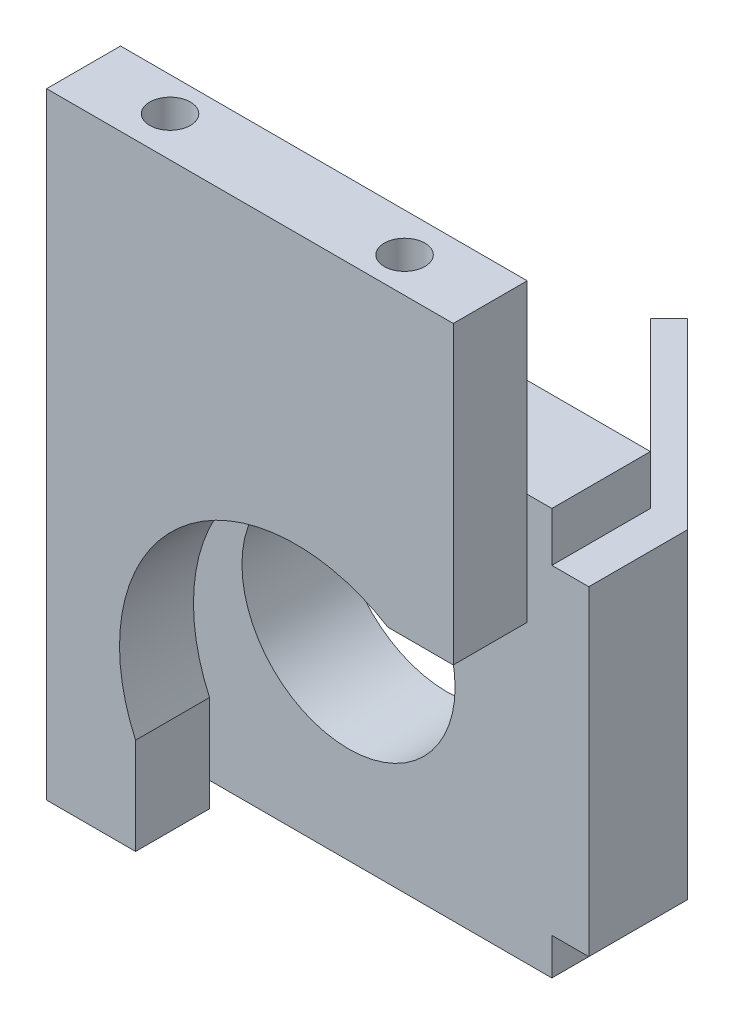
SolidWorks part; units mm, degrees
ref_plane "Front Plane" through (0, 0, 0) normal (0, 0, 1) x (1, 0, 0)
ref_plane "Top Plane" through (0, 0, 0) normal (0, 1, 0) x (1, 0, 0)
ref_plane "Right Plane" through (0, 0, 0) normal (1, 0, 0) x (0, 0, -1)
sketch "Sketch2" plane through (0, 0, 0) normal (0, 0, 1) x (1, 0, 0)
  line L1 (0, 0) -> (33, 0)
  line L2 (0, 0) -> (0, 33)
  line L3 (0, 33) -> (33, 33)
  line L4 (33, 0) -> (33, 33)
  circle A0 centre (16.5, 16.5) radius 8.65
  point P8 (16.5, 0)
  point P10 (0, 16.5)
  dimension "D3" = 17.3
  dimension "D1" = 33
  dimension "D2" = 33
extrude "Boss-Extrude1" add sketch "Sketch2" along normal blind 8
sketch "Sketch3" plane through (33, 0, 0) normal (1, 0, 0) x (0, 0, -1)
  line L0 (-8, 0) -> (-8, 33) construction
  line L1 (-8, 3) -> (0, 3)
  line L2 (-8, 3) -> (-8, 29)
  line L3 (-8, 29) -> (0, 29)
  line L4 (0, 3) -> (0, 29)
  line L5 (0, 0) -> (0, 33) construction
  line L6 (-8, 0) -> (0, 0) construction
  dimension "D1" = 26
  dimension "D2" = 3
extrude "Boss-Extrude2" add sketch "Sketch3" along normal blind 3
ref_plane "Plane1" through (16.5, 0, -16.5) normal (0.7071, 0, -0.7071) x (0, 1, 0)
sketch "Sketch4" plane through (16.5, 0, -16.5) normal (0.7071, 0, -0.7071) x (0, 1, 0)
  line L1 (3, 25.4558) -> (29, 25.4558)
  line L2 (3, 25.4558) -> (3, 4.4558)
  line L3 (3, 4.4558) -> (29, 4.4558)
  line L4 (29, 25.4558) -> (29, 4.4558)
  circle A0 centre (16, 14.9558) radius 8.1
  dimension "D3" = 16.2
  dimension "D1" = 21
  dimension "D2" = 26
  dimension "D4" = 10.5
  dimension "D5" = 13
extrude "Boss-Extrude3" add sketch "Sketch4" along normal blind 2.12
sketch "Sketch5" plane through (0, 0, 8) normal (0, 0, 1) x (1, 0, 0)
  line L0 (0, 33) -> (0, 0) construction
  line L1 (33, 33) -> (0, 33) construction
  circle A0 centre (2.5, 30.5) radius 1.5
  dimension "D1" = 3
  dimension "D2" = 2.5
  dimension "D3" = 2.5
extrude "Boss-Extrude4" add sketch "Sketch5" along normal blind 2
sketch "Sketch6" plane through (0, 0, 10) normal (0, 0, 1) x (1, 0, 0)
  line L0 (7.22, 0) -> (7.22, 7.8232)
  line L1 (0, 0) -> (7.22, 0)
  line L2 (0, 0) -> (0, 50)
  line L3 (0, 50) -> (33, 50)
  line L4 (33, 26) -> (33, 50)
  line L5 (33, 26) -> (27.6941, 26)
  arc A0 (7.22, 7.8232) -> (27.6941, 26) centre (20.2307, 13.7874) cw
  dimension "D5" = 20.2307
  dimension "D6" = 36.2126
  dimension "D7" = 14.3126
  dimension "D1" = 50
  dimension "D2" = 33
  dimension "D3" = 7.22
  dimension "D4" = 24
extrude "Boss-Extrude5" add sketch "Sketch6" along normal blind 6
sketch "Sketch7" plane through (0, 50, 0) normal (0, 1, 0) x (1, 0, 0)
  line L0 (0, -8) -> (0, 0) construction
  line L2 (33, -8) -> (33, 0) construction
  line L3 (33, -10) -> (0, -10) construction
  circle A0 centre (6.77, -12.75) radius 1.65
  circle A1 centre (26.2, -13.15) radius 1.65
  dimension "D1" = 3.3
  dimension "D4" = 3.3
  dimension "D2" = 6.77
  dimension "D3" = 2.75
  dimension "D5" = 3.15
  dimension "D6" = 6.8
extrude "Cut-Extrude1" cut sketch "Sketch7" against normal blind 10
